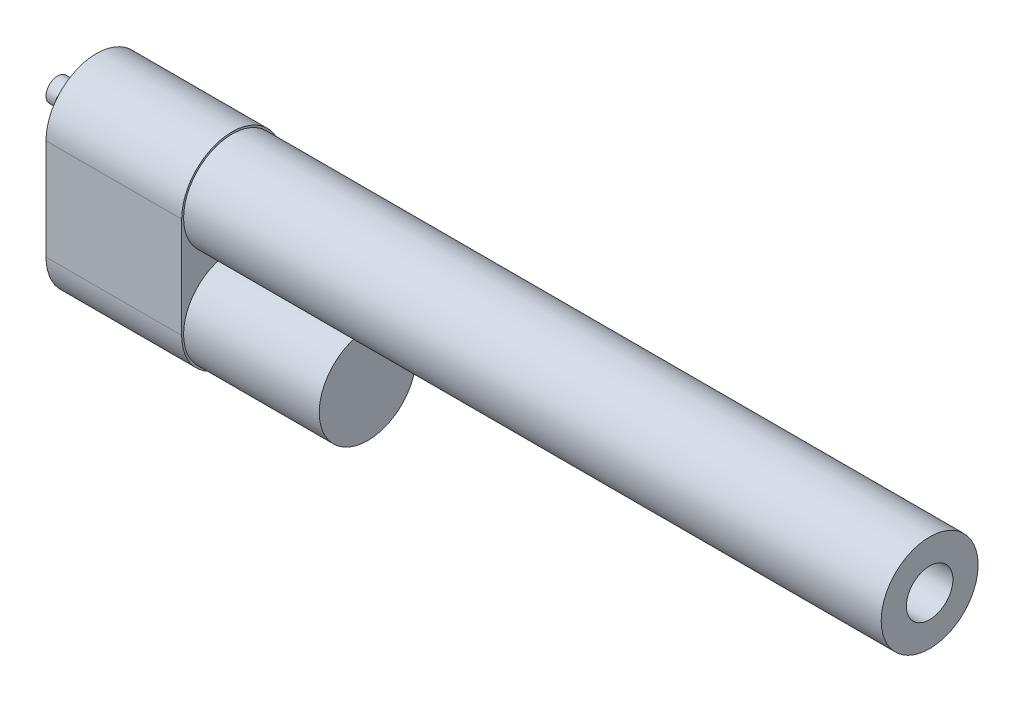
SolidWorks part; units mm, degrees
ref_plane "Front Plane" through (0, 0, 0) normal (0, 0, 1) x (1, 0, 0)
ref_plane "Top Plane" through (0, 0, 0) normal (0, 1, 0) x (1, 0, 0)
ref_plane "Right Plane" through (0, 0, 0) normal (1, 0, 0) x (0, 0, -1)
sketch "Sketch1" plane through (0, 0, 0) normal (0, 0, 1) x (1, 0, 0)
  line L0 (0, 0) -> (322.5655, 0) construction
  line L1 (0, 0) -> (0, 3)
  line L2 (0, 3) -> (10, 3)
  line L3 (10, 3) -> (10, 12.5)
  line L4 (10, 12.5) -> (225, 12.5)
  line L5 (225, 12.5) -> (225, 0)
  line L6 (0, 0) -> (225, 0)
  dimension "D1" = 3
  dimension "D2" = 12.5
  dimension "D3" = 10
  dimension "D4" = 215
revolve "Revolve1" add sketch "Sketch1" angle 360 about L0
sketch "Sketch2" plane through (225, 0, 0) normal (1, 0, 0) x (0, 0, -1)
  circle A0 centre (0, 0) radius 6
  dimension "D1" = 12
sketch "Sketch3" plane through (0, 0, 0) normal (0, 0, 1) x (1, 0, 0)
  line L0 (0, 3) -> (0, -3) construction
  circle A0 centre (5, 0) radius 2.5
  dimension "D1" = 5
  dimension "D2" = 5
extrude "Cut-Extrude2" cut sketch "Sketch3" against normal through all both and the other way through all
extrude "Cut-Extrude3" cut sketch "Sketch2" against normal blind 183
sketch "Sketch4" plane through (10, 0, 0) normal (-1, 0, 0) x (0, 0, 1)
  line L0 (-13, 0) -> (-13, -26)
  line L1 (13, 0) -> (13, -26)
  arc A0 (13, 0) -> (-13, 0) centre (0, 0) ccw
  arc A1 (-13, -26) -> (13, -26) centre (0, -26) ccw
  circle A2 centre (0, 0) radius 12.5
  dimension "D1" = 26
  dimension "D2" = 25
extrude "Boss-Extrude1" add sketch "Sketch4" against normal blind 35
sketch "Sketch5" plane through (45, 0, 0) normal (1, 0, 0) x (0, 0, -1)
  circle A0 centre (0, -26) radius 12.5
  dimension "D1" = 25
extrude "Boss-Extrude2" add sketch "Sketch5" along normal blind 35
